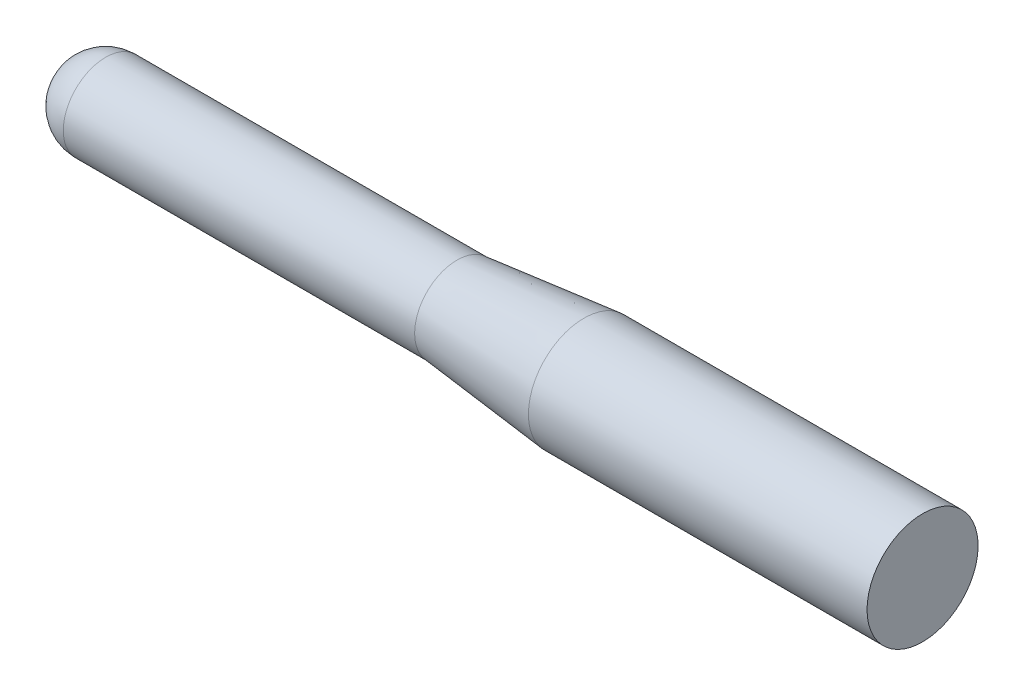
SolidWorks part; units mm, degrees
material "Tungsten"
ref_plane "Front Plane" through (0, 0, 0) normal (0, 0, 1) x (1, 0, 0)
ref_plane "Top Plane" through (0, 0, 0) normal (0, 1, 0) x (1, 0, 0)
ref_plane "Right Plane" through (0, 0, 0) normal (1, 0, 0) x (0, 0, -1)
sketch "Sketch1" plane through (0, 0, 0) normal (0, 0, 1) x (1, 0, 0)
  line L0 (0, 0) -> (257.81, 0) construction
  line L1 (12.7, 12.7) -> (118.11, 12.7)
  line L4 (118.11, 12.7) -> (156.21, 16.6623)
  line L5 (156.21, 16.6623) -> (257.81, 16.6623)
  line L6 (257.81, 16.6623) -> (257.81, 0)
  line L7 (118.11, 12.7) -> (156.21, 12.7) construction
  line L8 (156.21, 12.7) -> (156.21, 16.6623) construction
  line L9 (0, 0) -> (12.7, 0) construction
  line L10 (0, 0) -> (257.81, 0) construction
  line L11 (0, 0) -> (257.81, 0)
  arc A1 (12.7, 12.7) -> (0, 0) centre (12.7, 0) ccw
  dimension "D2" = 105.41
  dimension "D3" = 38.1
  dimension "D4" = 101.6
revolve "Revolve1" add sketch "Sketch1" angle 360 about L11
